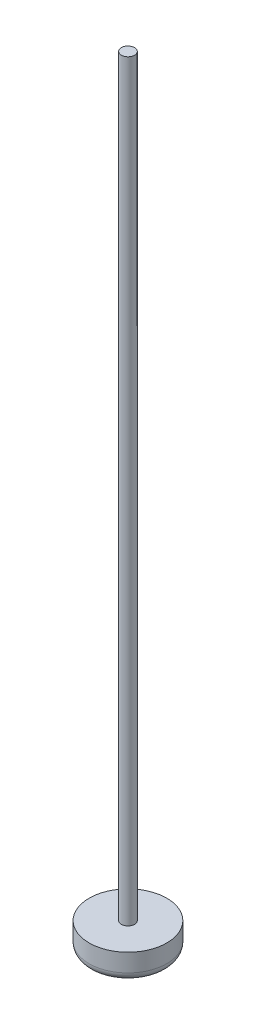
SolidWorks part; units mm, degrees
ref_plane "Front Plane" through (0, 0, 0) normal (0, 0, 1) x (1, 0, 0)
ref_plane "Top Plane" through (0, 0, 0) normal (0, 1, 0) x (1, 0, 0)
ref_plane "Right Plane" through (0, 0, 0) normal (1, 0, 0) x (0, 0, -1)
sketch "Sketch3" plane through (0, 0, 0) normal (0, 1, 0) x (1, 0, 0)
  circle A0 centre (0, 0) radius 4.6672
  dimension "D1" = 9.3345
extrude "Boss-Extrude1" add sketch "Sketch3" along normal blind 3.175
sketch "Sketch4" plane through (0, 3.175, 0) normal (0, 1, 0) x (1, 0, 0)
  circle A0 centre (0, 0) radius 0.7937
extrude "Boss-Extrude2" add sketch "Sketch4" along normal blind 90.4875
fillet "Fillet1" radius 1.016 1 edges at (0, 0, 4.6673)
